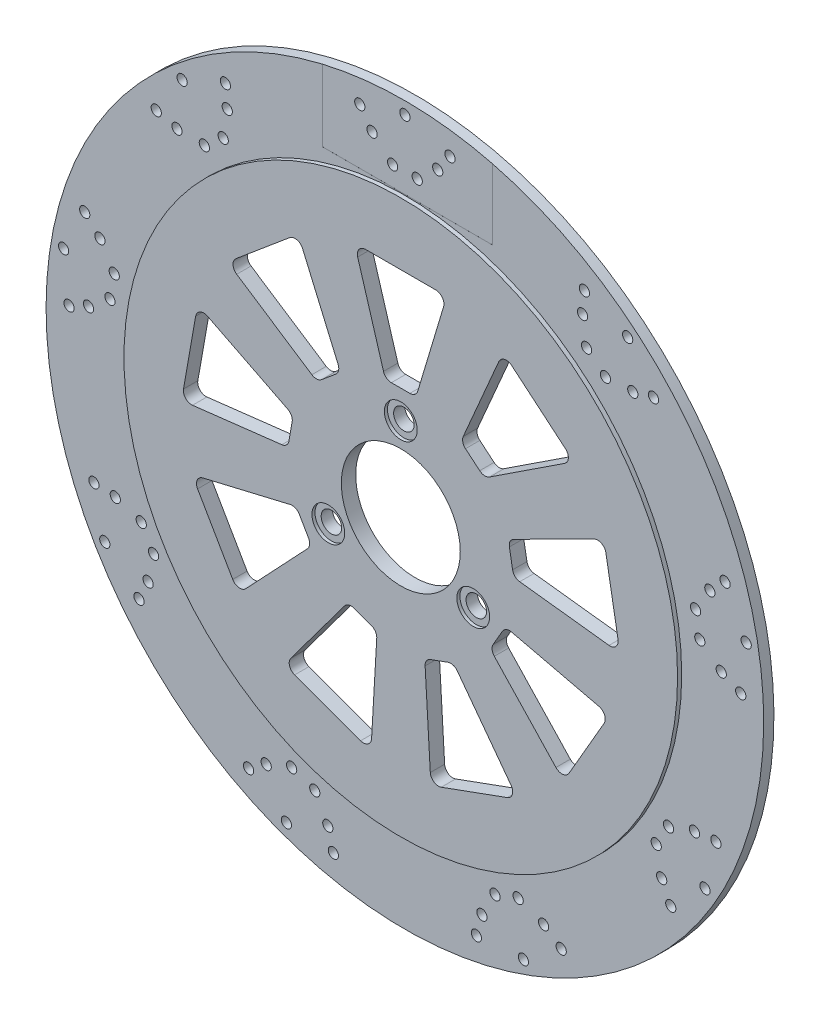
SolidWorks part; units mm, degrees
ref_plane "Płaszczyzna przednia" through (0, 0, 0) normal (0, 0, 1) x (1, 0, 0)
ref_plane "Płaszczyzna górna" through (0, 0, 0) normal (0, 1, 0) x (1, 0, 0)
ref_plane "Płaszczyzna prawa" through (0, 0, 0) normal (1, 0, 0) x (0, 0, -1)
sketch "Sketch1" plane through (0, 0, 0) normal (0, 0, 1) x (1, 0, 0)
  circle A0 centre (0, 0) radius 175
  circle A1 centre (0, 0) radius 29
  dimension "D1" = 350
  dimension "D2" = 58
extrude "Boss-Extrude1" add sketch "Sketch1" along normal blind 7
ref_plane "Plane1" through (0, 0, 7) normal (0, 0, 1) x (1, 0, 0)
sketch "Sketch2" plane through (0, 0, 7) normal (0, 0, 1) x (1, 0, 0)
  circle A0 centre (0, 0) radius 135
  circle A1 centre (0, 0) radius 175
  dimension "D1" = 270
  dimension "D2" = 350
extrude "Cut-Extrude1" cut sketch "Sketch2" against normal blind 2
sketch "Sketch3" plane through (0, 0, 7) normal (0, 0, 1) x (1, 0, 0)
  circle A0 centre (0, 0) radius 40.8 construction
  circle A1 centre (0, 40.8) radius 5
  dimension "D1" = 81.6
  dimension "D2" = 10
extrude "Cut-Extrude2" cut sketch "Sketch3" against normal through all
pattern_circular "CirPattern1" count 3 over 360 about axis through (0, 0, 0) along (0, 0, 1) of "Cut-Extrude2"
sketch "Sketch4" plane through (0, 0, 7) normal (0, 0, 1) x (1, 0, 0)
  circle A0 centre (0, 40.8) radius 8
  dimension "D1" = 16
extrude "Cut-Extrude3" cut sketch "Sketch4" against normal blind 1.5
pattern_circular "CirPattern2" count 3 over 360 about axis through (0, 0, 0) along (0, 0, 1) of "Cut-Extrude3"
sketch "Sketch5" plane through (0, 0, 7) normal (0, 0, 1) x (1, 0, 0)
  line L0 (-4.597, 54.5836) -> (4.4508, 54.5836)
  line L3 (-8.4283, 57.4342) -> (-21.0283, 99.4342)
  line L4 (8.2821, 57.4342) -> (20.8821, 99.4342)
  line L5 (-17.197, 104.5836) -> (17.0508, 104.5836)
  arc A0 (-4.597, 54.5836) -> (-8.4283, 57.4342) centre (-4.597, 58.5836) cw
  arc A1 (8.2821, 57.4342) -> (4.4508, 54.5836) centre (4.4508, 58.5836) cw
  arc A2 (20.8821, 99.4342) -> (17.0508, 104.5836) centre (17.0508, 100.5836) ccw
  arc A3 (-21.0283, 99.4342) -> (-17.197, 104.5836) centre (-17.197, 100.5836) cw
  point P7 (-7.5731, 54.5836)
  point P10 (7.4269, 54.5836)
  point P13 (22.4269, 104.5836)
  point P16 (-22.5731, 104.5836)
  dimension "D3" = 4
  dimension "D1" = 15
  dimension "D2" = 45
  dimension "D4" = 50
extrude "Cut-Extrude4" cut sketch "Sketch5" against normal through all
pattern_circular "CirPattern3" count 9 over 360 about axis through (0, 0, 0) along (0, 0, 1) of "Cut-Extrude4"
sketch "Sketch7" plane through (0, 0, 7) normal (0, 0, 1) x (1, 0, 0)
  circle A0 centre (-16, 153.8478) radius 2.5
  circle A1 centre (0, 169.0061) radius 2.5
  circle A2 centre (-6, 145.0061) radius 2.5
  circle A3 centre (6, 145.0061) radius 2.5
  circle A4 centre (16, 153.8478) radius 2.5
  circle A5 centre (-22, 162.4293) radius 2.5
  circle A6 centre (22, 162.4293) radius 2.5
  dimension "D2" = 5
extrude "Cut-Extrude5" cut sketch "Sketch7" against normal through all
pattern_circular "CirPattern4" count 9 over 360 about axis through (0, 0, 0) along (0, 0, 1) of "Cut-Extrude5"
sketch "Sketch8" plane through (0, 0, 0) normal (0, 0, 1) x (1, 0, 0)
  circle A0 centre (0, 0) radius 175
  circle A1 centre (0, 0) radius 135
  dimension "D1" = 270
extrude "Cut-Extrude6" cut sketch "Sketch8" along normal blind 0.01
ref_plane "Plane2" through (0, 0, 0.01) normal (0, 0, -1) x (-1, 0, 0)
sketch "Sketch13" plane through (0, 0, 0.01) normal (0, 0, -1) x (-1, 0, 0)
  line L1 (-38.4943, 175.5102) -> (40.7977, 175.5102)
  line L2 (-38.4943, 175.5102) -> (-38.4943, 135.6341)
  line L3 (-38.4943, 135.6341) -> (40.7977, 135.6341)
  line L4 (40.7977, 175.5102) -> (40.7977, 135.6341)
extrude "Cut-Extrude16" cut sketch "Sketch13" against normal blind 0.01
ref_plane "Plane3" through (0, 0, 5) normal (0, 0, 1) x (1, 0, 0)
sketch "Sketch14" plane through (0, 0, 5) normal (0, 0, 1) x (1, 0, 0)
  line L5 (-40.1743, 182.1162) -> (42.6959, 182.1162)
  line L6 (-40.1743, 182.1162) -> (-40.1743, 135.3983)
  line L7 (-40.1743, 135.3983) -> (42.6959, 135.3983)
  line L8 (42.6959, 182.1162) -> (42.6959, 135.3983)
extrude "Cut-Extrude17" cut sketch "Sketch14" against normal blind 0.01
